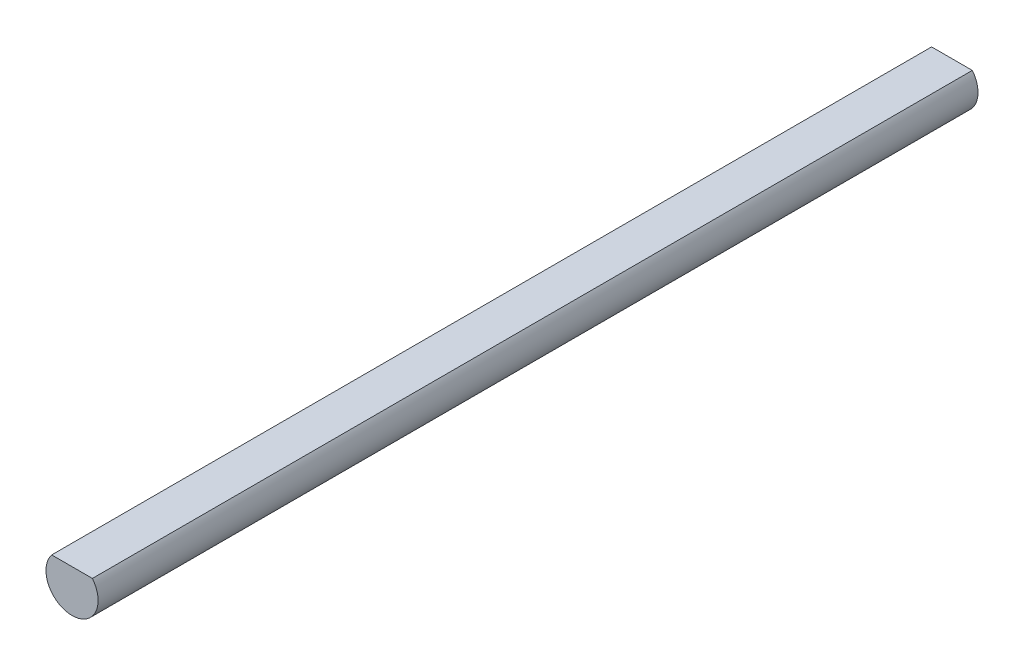
SolidWorks part; units mm, degrees
ref_plane "Front Plane" through (0, 0, 0) normal (0, 0, 1) x (1, 0, 0)
ref_plane "Top Plane" through (0, 0, 0) normal (0, 1, 0) x (1, 0, 0)
ref_plane "Right Plane" through (0, 0, 0) normal (1, 0, 0) x (0, 0, -1)
sketch "Sketch2" plane through (0, 0, 0) normal (0, 0, 1) x (1, 0, 0)
  circle A0 centre (0, 0) radius 4
  dimension "D1" = 8
extrude "Boss-Extrude1" add sketch "Sketch2" along normal blind 135
sketch "Sketch3" plane through (0, 0, 0) normal (0, 0, 1) x (1, 0, 0)
  line L0 (-3.1225, 2.5) -> (3.1225, 2.5)
  circle A0 centre (0, 0) radius 4 construction
  arc A1 (3.1225, 2.5) -> (-3.1225, 2.5) centre (0, 0) ccw
  dimension "D1" = 2.5
extrude "Cut-Extrude1" cut sketch "Sketch3" along normal through all both and the other way through all
